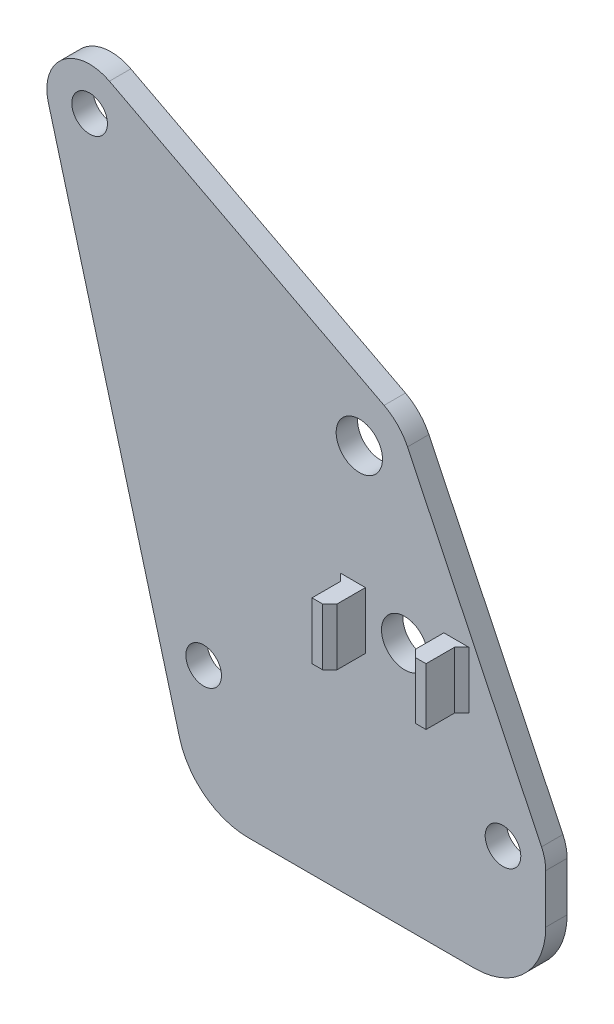
SolidWorks part; units mm, degrees
ref_plane "Front Plane" through (0, 0, 0) normal (0, 0, 1) x (1, 0, 0)
ref_plane "Top Plane" through (0, 0, 0) normal (0, 1, 0) x (1, 0, 0)
ref_plane "Right Plane" through (0, 0, 0) normal (1, 0, 0) x (0, 0, -1)
sketch "Sketch1" plane through (0, 0, 0) normal (0, 0, 1) x (1, 0, 0)
  line L0 (-174.1487, -16.8684) -> (5.8513, -16.8684) construction
  line L5 (-174.1487, -16.8684) -> (5.8513, -16.8684) construction
  line L6 (-58, 60) -> (-42, 0.929) construction
  line L7 (-42, 0.929) -> (0, 0) construction
  line L8 (0, 0) -> (-13.7985, 17.748) construction
  line L9 (-13.7985, 17.748) -> (-20.1576, 38.5476) construction
  line L10 (-20.1576, 38.5476) -> (-58, 60) construction
  line L11 (-58, 60) -> (0, 0) construction
  line L12 (-63.7913, 58.4314) -> (-43.3956, -16.8684)
  line L13 (-55.2228, 65.3186) -> (-16.6861, 45.1959)
  line L14 (-13.3956, 41.7918) -> (5.4096, 2.5954)
  line L15 (6, 0) -> (6, -16.8684)
  line L16 (-43.3956, -16.8684) -> (6, -16.8684)
  circle A0 centre (0, 0) radius 2.5
  circle A1 centre (-58, 60) radius 2.5
  circle A2 centre (-42, 0.929) radius 2.5 construction
  circle A3 centre (-42, 0.929) radius 2.5
  circle A4 centre (-13.7985, 17.748) radius 3.8 construction
  circle A5 centre (-13.7985, 17.748) radius 3.8 construction
  circle A6 centre (-20.1576, 38.5476) radius 10 construction
  circle A7 centre (-20.1576, 38.5476) radius 10 construction
  circle A8 centre (-20.1576, 38.5476) radius 3.25
  circle A9 centre (-42, 0.929) radius 6 construction
  circle A10 centre (-58, 60) radius 6 construction
  circle A11 centre (-20.1576, 38.5476) radius 7.5 construction
  circle A12 centre (0, 0) radius 6 construction
  arc A13 (-63.7913, 58.4314) -> (-55.2228, 65.3186) centre (-58, 60) cw
  arc A14 (-16.6861, 45.1959) -> (-13.3956, 41.7918) centre (-20.1576, 38.5476) cw
  arc A15 (5.4096, 2.5954) -> (6, 0) centre (0, 0) cw
  circle A16 centre (-13.7985, 17.748) radius 3.25
  dimension "D1" = 5
  dimension "D4" = 6.5
  dimension "D5" = 12
  dimension "D6" = 15
  dimension "D7" = 6.5
  dimension "D2" = 58
  dimension "D3" = 60
extrude "Boss-Extrude1" add sketch "Sketch1" along normal blind 3
sketch "Sketch2" plane through (0, 0, 3) normal (0, 0, 1) x (1, 0, 0)
  line L0 (-8.2985, 21.748) -> (-5.7985, 21.748)
  line L1 (-19.2985, 21.748) -> (-8.2985, 21.748) construction
  line L2 (-19.2985, 21.748) -> (-19.2985, 13.748)
  line L3 (-19.2985, 13.748) -> (-8.2985, 13.748) construction
  line L4 (-8.2985, 21.748) -> (-8.2985, 13.748)
  line L5 (-13.7985, 13.748) -> (-13.7985, 21.748) construction
  line L6 (-19.2985, 17.748) -> (-8.2985, 17.748) construction
  line L7 (-5.7985, 21.748) -> (-5.7985, 13.748)
  line L8 (-5.7985, 13.748) -> (-8.2985, 13.748)
  line L9 (-19.2985, 13.748) -> (-21.7985, 13.748)
  line L10 (-21.7985, 13.748) -> (-21.7985, 21.748)
  line L11 (-21.7985, 21.748) -> (-19.2985, 21.748)
  point P0 (-13.7985, 17.748)
  dimension "D1" = 11
  dimension "D2" = 2.5
  dimension "D3" = 8
extrude "Boss-Extrude2" add sketch "Sketch2" along normal blind 5
chamfer "Chamfer1" distance 1 angle 45 4 edges at (-19.2985, 17.748, 8) (-8.2985, 17.748, 8) (-21.7985, 17.748, 3) (-5.7985, 17.748, 3)
fillet "Fillet1" radius 10 2 edges at (-43.3956, -16.8684, 1.5) (6, -16.8684, 1.5)
